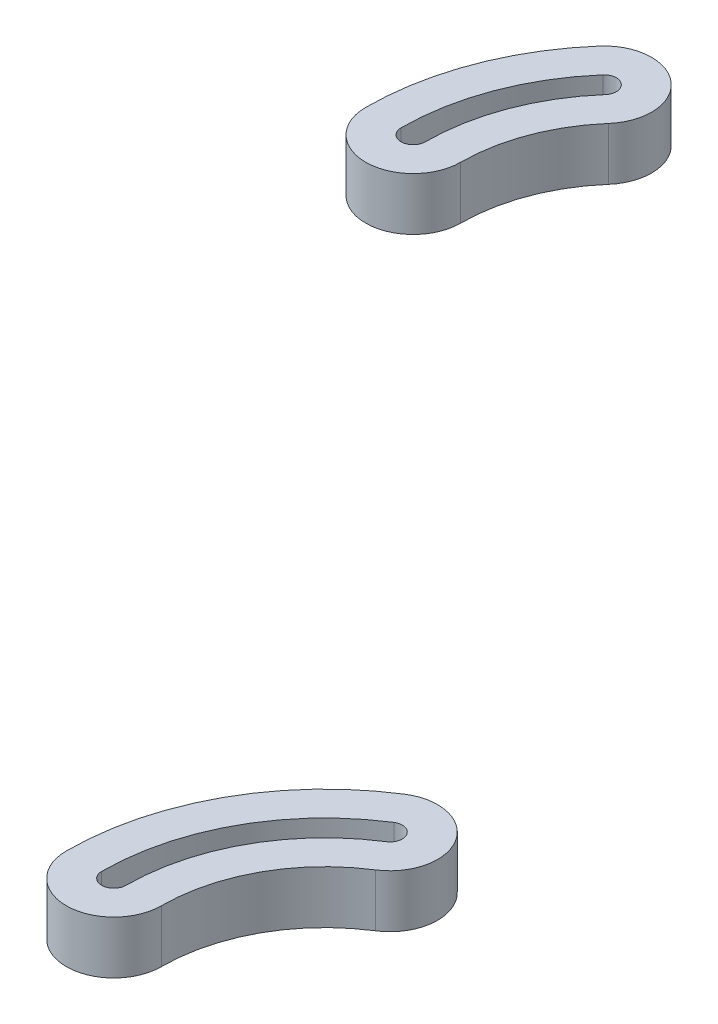
SolidWorks part; units mm, degrees
material "ABS"
ref_plane "Płaszczyzna XY" through (0, 0, 0) normal (0, 0, 1) x (1, 0, 0)
ref_plane "Płaszczyzna XZ" through (0, 0, 0) normal (0, 1, 0) x (1, 0, 0)
ref_plane "Płaszczyzna YZ" through (0, 0, 0) normal (1, 0, 0) x (0, 0, -1)
sketch "Szkic1" plane through (0, 455.3, 0) normal (0, 1, 0) x (1, 0, 0)
  arc A0 (-111.7627, -370.5444) -> (-134.5135, -411.9205) centre (-85.5135, -411.9205) ccw construction
  arc A1 (-102.1201, -385.7438) -> (-116.5135, -411.9205) centre (-85.5135, -411.9205) ccw construction
  arc A2 (-134.5135, -411.9205) -> (-116.5135, -411.9205) centre (-125.5135, -411.9205) ccw construction
  arc A3 (-102.1201, -385.7438) -> (-111.7627, -370.5444) centre (-106.9414, -378.1441) ccw construction
  arc A4 (-228.1662, -261.5446) -> (-210.1662, -261.5446) centre (-219.1662, -261.5446) ccw construction
  arc A5 (-202.5154, -241.153) -> (-210.1662, -261.5446) centre (-179.1662, -261.5446) ccw construction
  arc A6 (-216.073, -229.3127) -> (-228.1662, -261.5446) centre (-179.1662, -261.5446) ccw construction
  arc A7 (-202.5154, -241.153) -> (-216.073, -229.3127) centre (-209.2942, -235.2328) ccw construction
  arc A8 (-111.7627, -370.5444) -> (-134.5135, -411.9205) centre (-85.5135, -411.9205) ccw
  arc A9 (-102.1201, -385.7438) -> (-116.5135, -411.9205) centre (-85.5135, -411.9205) ccw
  arc A10 (-134.5135, -411.9205) -> (-116.5135, -411.9205) centre (-125.5135, -411.9205) ccw
  arc A11 (-102.1201, -385.7438) -> (-111.7627, -370.5444) centre (-106.9414, -378.1441) ccw
  arc A12 (-228.1662, -261.5446) -> (-210.1662, -261.5446) centre (-219.1662, -261.5446) ccw
  arc A13 (-202.5154, -241.153) -> (-210.1662, -261.5446) centre (-179.1662, -261.5446) ccw
  arc A14 (-216.073, -229.3127) -> (-228.1662, -261.5446) centre (-179.1662, -261.5446) ccw
  arc A15 (-202.5154, -241.153) -> (-216.073, -229.3127) centre (-209.2942, -235.2328) ccw
  arc A16 (-105.7093, -380.0863) -> (-108.1735, -376.202) centre (-106.9414, -378.1441) ccw
  arc A17 (-127.8135, -411.9205) -> (-123.2135, -411.9205) centre (-125.5135, -411.9205) ccw
  arc A18 (-105.7093, -380.0863) -> (-123.2135, -411.9205) centre (-85.5135, -411.9205) ccw
  arc A19 (-108.1735, -376.202) -> (-127.8135, -411.9205) centre (-85.5135, -411.9205) ccw
  arc A20 (-207.5618, -236.7457) -> (-211.0265, -233.7199) centre (-209.2942, -235.2328) ccw
  arc A21 (-221.4662, -261.5446) -> (-216.8662, -261.5446) centre (-219.1662, -261.5446) ccw
  arc A22 (-207.5618, -236.7457) -> (-216.8662, -261.5446) centre (-179.1662, -261.5446) ccw
  arc A23 (-211.0265, -233.7199) -> (-221.4662, -261.5446) centre (-179.1662, -261.5446) ccw
  dimension "D1" = 4.6
  dimension "D2" = 4.6
  dimension "D3" = 4.6
  dimension "D4" = 4.6
extrude "Dodanie-wyciągnięcie1" add sketch "Szkic1" against normal blind 10
